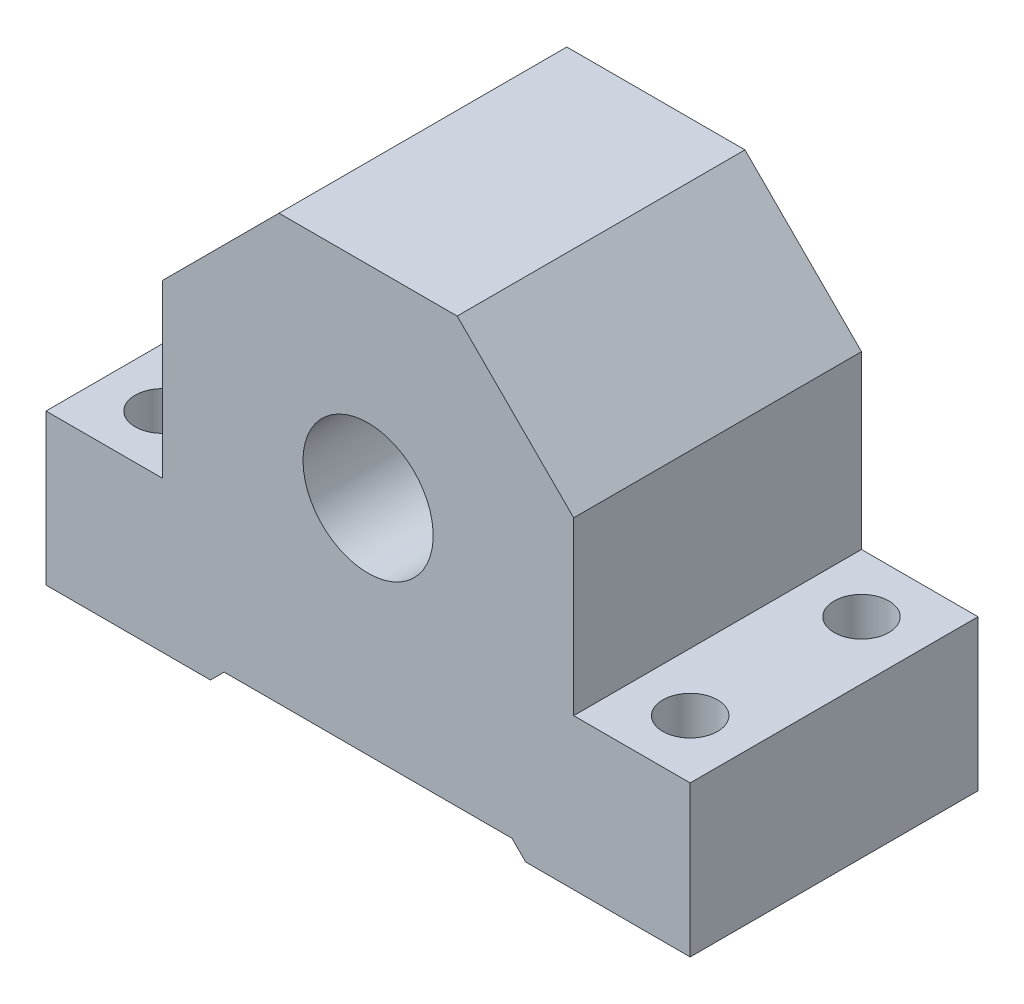
SolidWorks part; units mm, degrees
ref_plane "Płaszczyzna przednia" through (0, 0, 0) normal (0, 0, 1) x (1, 0, 0)
ref_plane "Płaszczyzna górna" through (0, 0, 0) normal (0, 1, 0) x (1, 0, 0)
ref_plane "Płaszczyzna prawa" through (0, 0, 0) normal (1, 0, 0) x (0, 0, -1)
sketch "Szkic1" plane through (0, 0, 0) normal (0, 0, 1) x (1, 0, 0)
  line L0 (-47, 11) -> (-30, 11)
  line L2 (47, -11) -> (47, 11)
  line L4 (-47, -11) -> (-47, 11)
  line L5 (47, -11) -> (-47, 11) construction
  line L6 (47, 11) -> (-47, -11) construction
  line L7 (-30, 11) -> (-30, 36)
  line L8 (-30, 36) -> (-13, 53)
  line L9 (-13, 53) -> (13, 53)
  line L10 (13, 53) -> (30, 36)
  line L11 (30, 36) -> (30, 11)
  line L12 (30, 11) -> (47, 11)
  line L13 (-47, -11) -> (-23, -11)
  line L14 (-23, -11) -> (-21, -9)
  line L15 (-21, -9) -> (21, -9)
  line L16 (21, -9) -> (23, -11)
  line L17 (23, -11) -> (47, -11)
  point P0 (0, 0)
  point P5 (0, 0)
  point P18 (35, -11)
  dimension "D1" = 94
  dimension "D2" = 26
  dimension "D3" = 26
  dimension "D4" = 135
  dimension "D5" = 135
  dimension "D6" = 17
  dimension "D7" = 26
  dimension "D8" = 2
  dimension "D9" = 135
  dimension "D10" = 135
  dimension "D11" = 64
  dimension "D12" = 22
  dimension "D13" = 60
  dimension "D14" = 17
  dimension "D15" = 17
extrude "Dodanie-wyciągnięcie1" add sketch "Szkic1" along normal blind 42
sketch "Szkic2" plane through (0, 0, 0) normal (0, 0, -1) x (-1, 0, 0)
  line L0 (-13, 53) -> (13, 53) construction
  circle A0 centre (0, 23.5) radius 9.5
  point P4 (0, 0)
  point P6 (0, 0)
  dimension "D1" = 29.5
  dimension "D2" = 19
extrude "Wytnij-wyciągnięcie1" cut sketch "Szkic2" against normal blind 42
sketch "Szkic3" plane through (0, 11, 0) normal (0, 1, 0) x (1, 0, 0)
  line L0 (-30, 0) -> (-47, 0) construction
  line L1 (-47, -42) -> (-47, 0) construction
  line L2 (-30, -42) -> (-47, -42) construction
  line L3 (47, -42) -> (47, 0) construction
  line L6 (47, 0) -> (30, 0) construction
  line L7 (47, -42) -> (30, -42) construction
  circle A0 centre (-38.5, -8.5) radius 4
  circle A1 centre (-38.5, -33.5) radius 4
  circle A2 centre (38.5, -33.5) radius 4
  circle A3 centre (38.5, -8.5) radius 4
  dimension "D1" = 8.5
  dimension "D9" = 8
  dimension "D10" = 8
  dimension "D11" = 8
  dimension "D12" = 8
  dimension "D2" = 8.5
  dimension "D3" = 8.5
  dimension "D4" = 8.5
  dimension "D5" = 8.5
  dimension "D6" = 8.5
  dimension "D7" = 8.5
  dimension "D8" = 8.5
extrude "Wytnij-wyciągnięcie2" cut sketch "Szkic3" against normal blind 22
